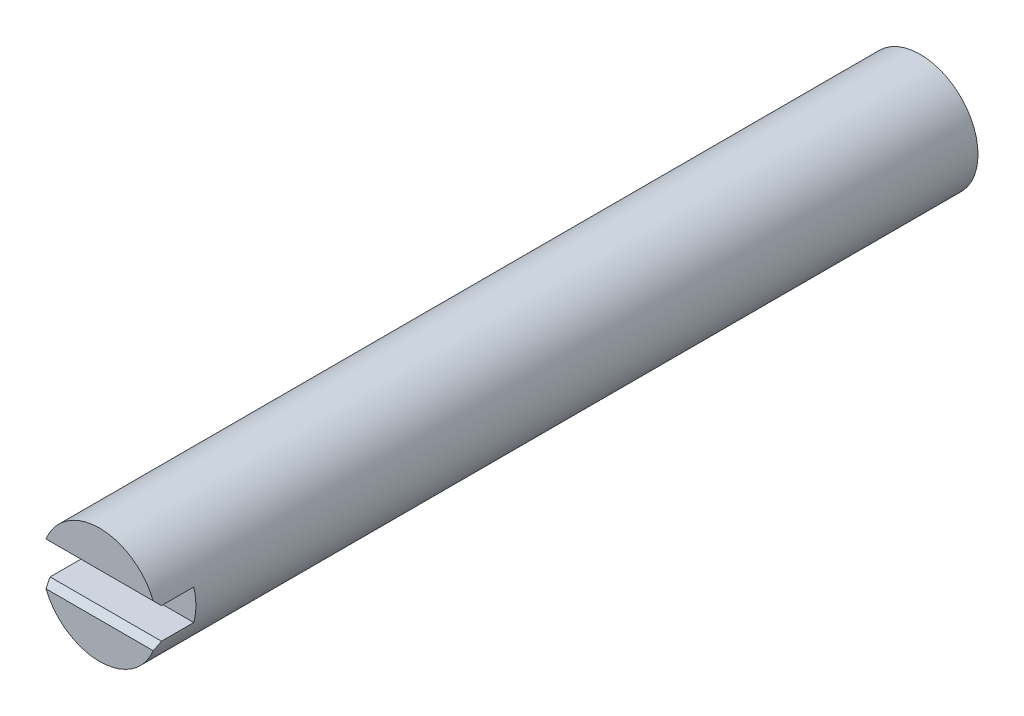
SolidWorks part; units mm, degrees
material "Plain Carbon Steel"
ref_plane "Front Plane" through (0, 0, 0) normal (0, 0, 1) x (1, 0, 0)
ref_plane "Top Plane" through (0, 0, 0) normal (0, 1, 0) x (1, 0, 0)
ref_plane "Right Plane" through (0, 0, 0) normal (1, 0, 0) x (0, 0, -1)
sketch "Sketch1" plane through (0, 0, 0) normal (0, 0, 1) x (1, 0, 0)
  circle A0 centre (0, 0) radius 4.7625
  dimension "D1" = 9.525
extrude "Boss-Extrude1" add sketch "Sketch1" against normal blind 67.6402
sketch "Sketch2" plane through (0, 0, 0) normal (0, 0, 1) x (1, 0, 0)
  line L1 (4.7625, -1.27) -> (-4.7625, -1.27)
  line L2 (4.7625, -1.27) -> (4.7625, 1.27)
  line L3 (4.7625, 1.27) -> (-4.7625, 1.27)
  line L4 (-4.7625, -1.27) -> (-4.7625, 1.27)
  line L5 (4.7625, -1.27) -> (-4.7625, 1.27) construction
  line L6 (4.7625, 1.27) -> (-4.7625, -1.27) construction
  circle A0 centre (0, 0) radius 4.7625 construction
  point P1 (0, 0)
  dimension "D2" = 2.54
extrude "Cut-Extrude1" cut sketch "Sketch2" against normal blind 3.175
chamfer "Chamfer1" distance 0.508 angle 45 2 edges at (0, -1.27, 0) (0, 1.27, 0)
